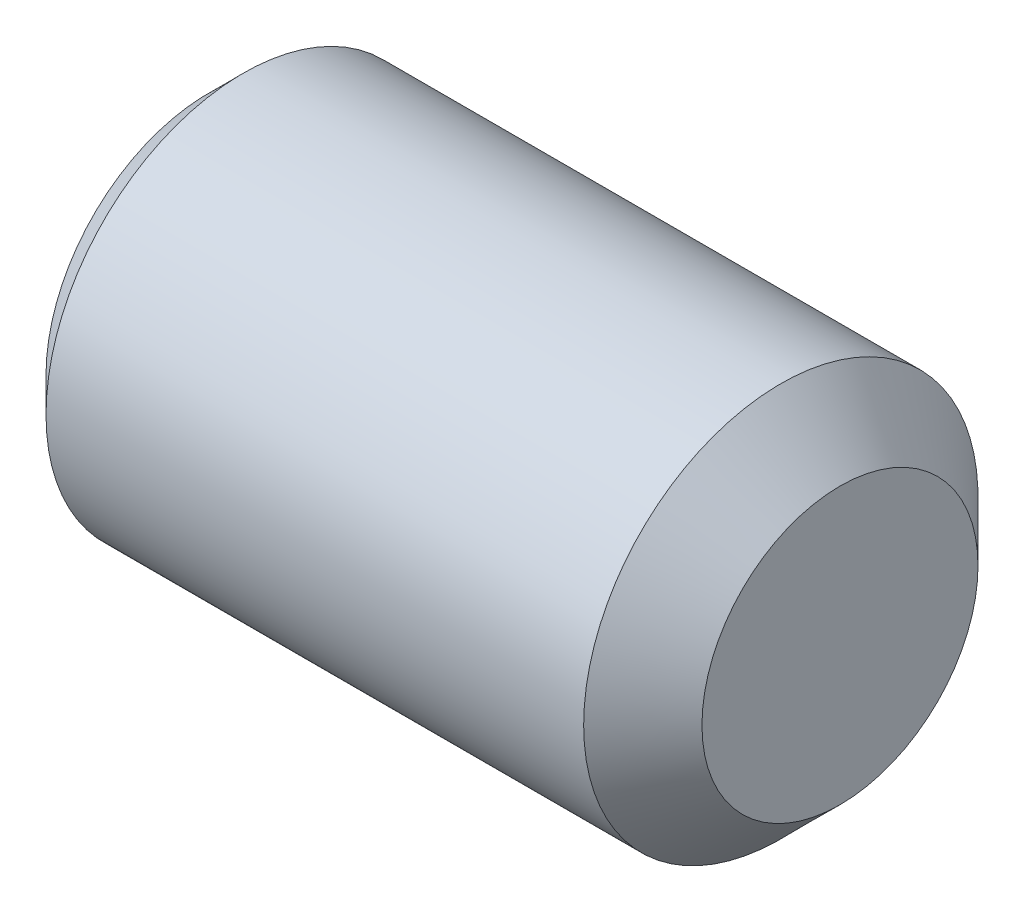
SolidWorks part; units mm, degrees
ref_plane "Front" through (0, 0, 0) normal (0, 0, 1) x (1, 0, 0)
ref_plane "Top" through (0, 0, 0) normal (0, 1, 0) x (1, 0, 0)
ref_plane "Right" through (0, 0, 0) normal (1, 0, 0) x (0, 0, -1)
sketch "Sketch1" plane through (0, 0, 0) normal (0, 0, 1) x (1, 0, 0)
  line L0 (0, 0) -> (8, 0)
  line L1 (8, 0) -> (8, 1.75)
  line L2 (8, 1.75) -> (7.25, 2.5)
  line L3 (7.25, 2.5) -> (0.433, 2.5)
  line L4 (0.433, 2.5) -> (0, 2.067)
  line L5 (0, 2.067) -> (0, 0)
  line L6 (-10.745, 0) -> (0.8952, 0) construction
  dimension "D1" = 45
  dimension "l" = 8
  dimension "D2" = 45
  dimension "dp" = 3.5
  dimension "d" = 5
  dimension "df" = 4.134
revolve "Base" add sketch "Sketch1" angle 360 about L6
cosmetic thread "ThreadCosmetic1" [suppressed] parameters "D2"=4.134
sketch "Sketch2" plane through (0, -0.0219, 0.0101) normal (-1, 0, 0) x (0, 0, 1)
  line L1 (1.4332, 0.0219) -> (0.7115, 1.2719)
  line L2 (0.7115, 1.2719) -> (-0.7318, 1.2719)
  line L3 (-0.7318, 1.2719) -> (-1.4535, 0.0219)
  line L4 (-1.4535, 0.0219) -> (-0.7318, -1.2281)
  line L5 (-0.7318, -1.2281) -> (0.7115, -1.2281)
  line L6 (0.7115, -1.2281) -> (1.4332, 0.0219)
  circle A0 centre (-0.0101, 0.0219) radius 1.25 construction
  dimension "s" = 2.5
extrude "HexagonSocket" cut sketch "Sketch2" against normal blind 2
sketch "Sketch3" plane through (0, 0, 0) normal (0, 0, 1) x (1, 0, 0)
  line L0 (-3.1441, 0) -> (0.1622, 0) construction
  line L2 (2, 1.25) -> (2.7217, 0)
  line L4 (2, 1.25) -> (2, 0)
  line L5 (2, 0) -> (2.7217, 0)
  dimension "D1" = 60
revolve "Cut-Revolve1" cut sketch "Sketch3" angle 360 about L0
sketch "Sketch4" plane through (0, 0, 0) normal (0, 0, 1) x (1, 0, 0)
  line L0 (0.433, 2.125) -> (0.6495, 2.5)
  line L1 (0.6495, 2.5) -> (0.6495, 2.933)
  line L2 (0.6495, 2.933) -> (0.2165, 2.933)
  line L3 (0.2165, 2.933) -> (0.2165, 2.5)
  line L4 (0.2165, 2.5) -> (0.433, 2.125)
  line L5 (0, 0) -> (0.9616, 0) construction
  line L6 (0.433, 2.5) -> (0.433, -2.5) construction
  dimension "D1" = 5
  dimension "D2" = 0.433
revolve "Cut-Revolve10" [suppressed] cut sketch "Sketch4" angle 360 about L5
pattern_linear "LPattern10" [suppressed] count 15 spacing 0.5196 along (1, 0, 0)
equation "\"df@Sketch1\" = \"D2@ThreadCosmetic1\""
equation "\"D1@Sketch4\" = \"d@Sketch1\""
equation "\"D2@Sketch4\" =  ( \"d@Sketch1\" - \"D2@ThreadCosmetic1\" )  / 2"
equation "\"D3@LPattern10\" = \"D2@Sketch4\" * 1.2"
equation "\"D1@LPattern10\" = (  \"l@Sketch1\" -  ( \"d@Sketch1\" - \"df@Sketch1\" )  / 2 )  / \"D3@LPattern10\""
